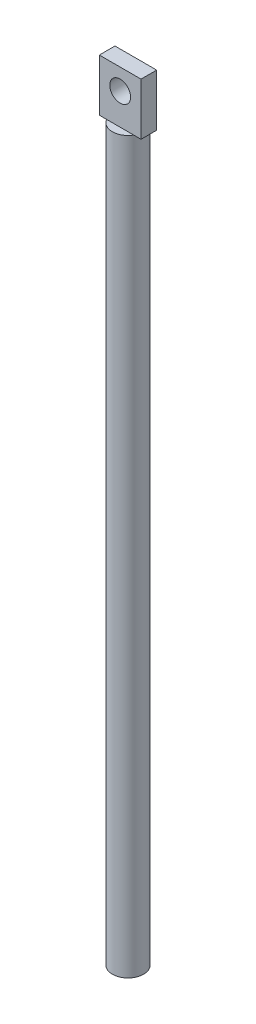
SolidWorks part; units mm, degrees
ref_plane "Front Plane" through (0, 0, 0) normal (0, 0, 1) x (1, 0, 0)
ref_plane "Top Plane" through (0, 0, 0) normal (0, 1, 0) x (1, 0, 0)
ref_plane "Right Plane" through (0, 0, 0) normal (1, 0, 0) x (0, 0, -1)
sketch "Sketch1" plane through (0, 0, 0) normal (0, 1, 0) x (1, 0, 0)
  circle A0 centre (0, 0) radius 1.5
  dimension "D1" = 3
extrude "Boss-Extrude1" add sketch "Sketch1" along normal blind 70
sketch "Sketch2" plane through (0, 70, 0) normal (0, 1, 0) x (1, 0, 0)
  line L1 (-2, 0.75) -> (2, 0.75)
  line L2 (-2, 0.75) -> (-2, -0.75)
  line L3 (-2, -0.75) -> (2, -0.75)
  line L4 (2, 0.75) -> (2, -0.75)
  line L5 (-2, 0.75) -> (2, -0.75) construction
  line L6 (-2, -0.75) -> (2, 0.75) construction
  point P0 (0, 0)
  dimension "D1" = 1.5
  dimension "D2" = 4
extrude "Boss-Extrude2" add sketch "Sketch2" along normal blind 5
sketch "Sketch3" plane through (0, 0, -0.75) normal (0, 0, -1) x (-1, 0, 0)
  line L0 (-2, 75) -> (2, 75) construction
  circle A0 centre (0, 73) radius 1
  dimension "D1" = 2
  dimension "D2" = 2
extrude "Cut-Extrude1" cut sketch "Sketch3" against normal through all
